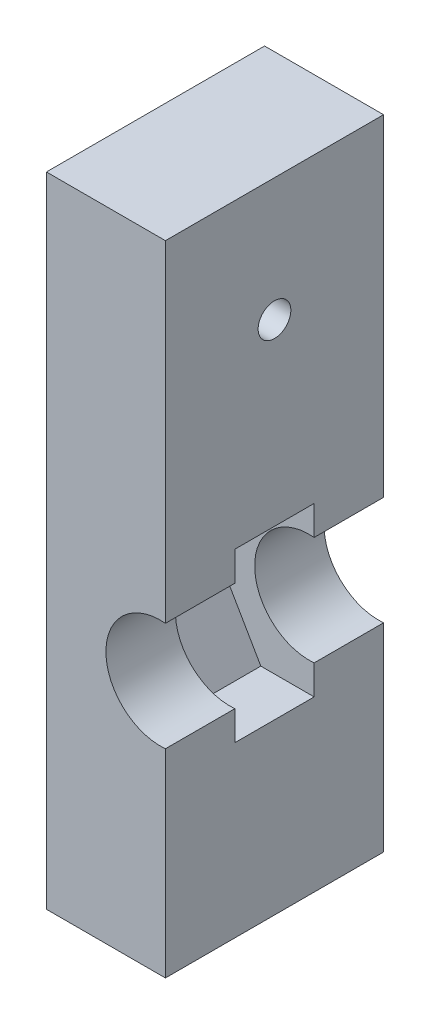
SolidWorks part; units mm, degrees
ref_plane "前基準面" through (0, 0, 0) normal (0, 0, 1) x (1, 0, 0)
ref_plane "上基準面" through (0, 0, 0) normal (0, 1, 0) x (1, 0, 0)
ref_plane "右基準面" through (0, 0, 0) normal (1, 0, 0) x (0, 0, -1)
sketch "草圖1" plane through (0, 0, 0) normal (0, 0, 1) x (1, 0, 0)
  line L0 (-0.3675, -59.7793) -> (-0.3675, -34.2793) construction
  line L1 (-11.8675, 4.6207) -> (11.1325, 4.6207)
  line L2 (-11.8675, 4.6207) -> (-11.8675, -59.7793)
  line L3 (-11.8675, -59.7793) -> (11.1325, -59.7793)
  line L4 (11.1325, 4.6207) -> (11.1325, -59.7793)
  line L5 (-7.6854, -30.0543) -> (6.9504, -38.5043) construction
  line L6 (9.3897, -34.2793) -> (4.5111, -25.8293)
  line L7 (4.5111, -25.8293) -> (-5.2461, -25.8293)
  line L8 (-5.2461, -25.8293) -> (-10.1247, -34.2793)
  line L9 (-10.1247, -34.2793) -> (-5.2461, -42.7293)
  line L10 (-5.2461, -42.7293) -> (4.5111, -42.7293)
  line L11 (4.5111, -42.7293) -> (9.3897, -34.2793)
  circle A0 centre (-0.3675, -34.2793) radius 8.45 construction
  dimension "D1" = 23
  dimension "D2" = 64.4
  dimension "D3" = 25.5
  dimension "D4" = 16.9
extrude "填料-伸長1" add sketch "草圖1" along normal blind 8
sketch "草圖3" plane through (0, 0, 8) normal (0, 0, 1) x (1, 0, 0)
  line L0 (-0.3675, -59.7793) -> (-0.3675, -34.2793) construction
  line L1 (-11.8675, 4.6207) -> (11.1325, 4.6207)
  line L2 (-11.8675, 4.6207) -> (-11.8675, -59.7793)
  line L3 (-11.8675, -59.7793) -> (11.1325, -59.7793)
  line L4 (11.1325, 4.6207) -> (11.1325, -59.7793)
  circle A0 centre (-0.3675, -34.2793) radius 5.5
  dimension "D1" = 25.5
  dimension "D2" = 11
extrude "填料-伸長2" add sketch "草圖3" along normal blind 7
sketch "草圖4" plane through (0, 0, 0) normal (0, 0, -1) x (-1, 0, 0)
  line L0 (0.3675, -59.7793) -> (0.3675, -34.2793) construction
  line L1 (-11.1325, 4.6207) -> (11.8675, 4.6207)
  line L2 (-11.1325, 4.6207) -> (-11.1325, -59.7793)
  line L3 (-11.1325, -59.7793) -> (11.8675, -59.7793)
  line L4 (11.8675, 4.6207) -> (11.8675, -59.7793)
  circle A0 centre (0.3675, -34.2793) radius 5.5
extrude "填料-伸長3" add sketch "草圖4" along normal blind 7
sketch "草圖5" plane through (11.1325, 0, 0) normal (1, 0, 0) x (0, 0, -1)
  line L0 (-4, -59.7793) -> (-4, -7.7793) construction
  line L1 (-15, -59.7793) -> (7, -59.7793) construction
  circle A0 centre (-4, -7.7793) radius 1.65
  dimension "D2" = 3.3
  dimension "D1" = 52
extrude "除料-伸長1" cut sketch "草圖5" against normal through all
sketch "草圖6" plane through (11.1325, 0, 0) normal (1, 0, 0) x (0, 0, -1)
  line L1 (-15, 4.6207) -> (7, 4.6207)
  line L2 (-15, 4.6207) -> (-15, -59.7793)
  line L3 (-15, -59.7793) -> (7, -59.7793)
  line L4 (7, 4.6207) -> (7, -59.7793)
extrude "除料-伸長2" cut sketch "草圖6" against normal blind 11
